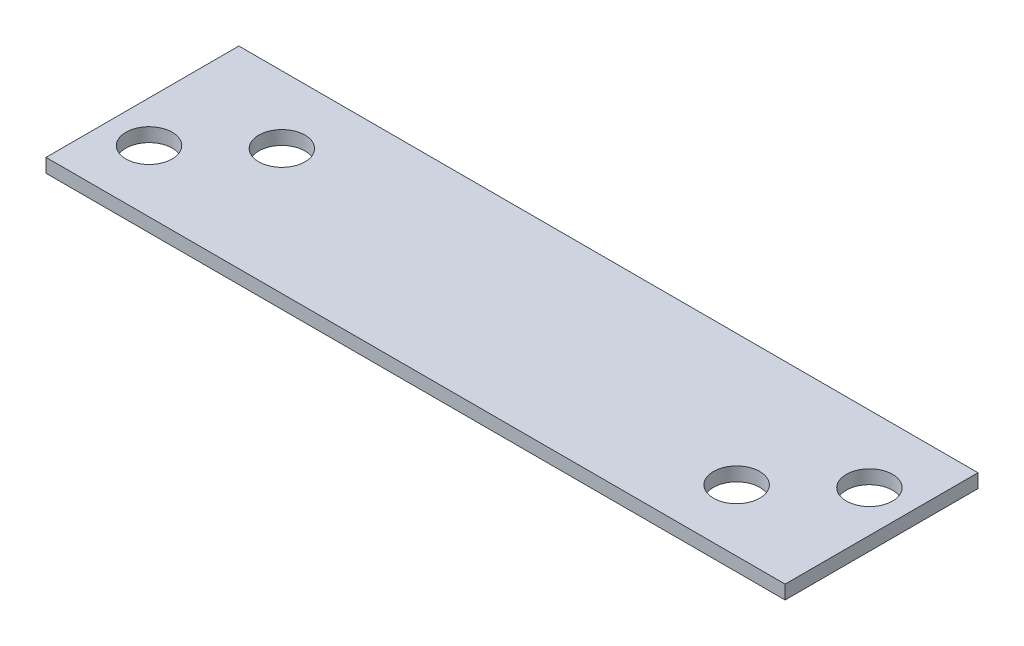
SolidWorks part; units mm, degrees
material "6061-T6 (SS)"
ref_plane "Front" through (0, 0, 0) normal (0, 0, 1) x (1, 0, 0)
ref_plane "Top" through (0, 0, 0) normal (0, 1, 0) x (1, 0, 0)
ref_plane "Right" through (0, 0, 0) normal (1, 0, 0) x (0, 0, -1)
sketch "Sketch1" plane through (0, 0, 0) normal (0, 1, 0) x (1, 0, 0)
  line L1 (0, 0) -> (85.1662, 0)
  line L2 (0, 0) -> (0, 22.225)
  line L3 (0, 22.225) -> (85.1662, 22.225)
  line L4 (85.1662, 0) -> (85.1662, 22.225)
  line L5 (0, 0) -> (85.1662, 22.225) construction
  line L6 (0, 22.225) -> (85.1662, 0) construction
  point P4 (42.5831, 11.1125)
  dimension "D1" = 22.225
  dimension "D2" = 85.1662
extrude "Boss-Extrude1" add sketch "Sketch1" along normal blind 1.5875
sketch "Sketch2" plane through (0, 0, 0) normal (0, -1, 0) x (1, 0, 0)
  circle A0 centre (4.7625, -7.112) radius 2.667 construction
  circle A1 centre (4.7625, -7.112) radius 2.667
  circle A2 centre (12.7, -14.478) radius 2.667 construction
  circle A3 centre (12.7, -14.478) radius 2.667
  circle A4 centre (72.4662, -7.112) radius 2.667 construction
  circle A5 centre (72.4662, -7.112) radius 2.667
  circle A6 centre (80.4037, -14.478) radius 2.667 construction
  circle A7 centre (80.4037, -14.478) radius 2.667
extrude "Cut-Extrude1" cut sketch "Sketch2" against normal up to next
